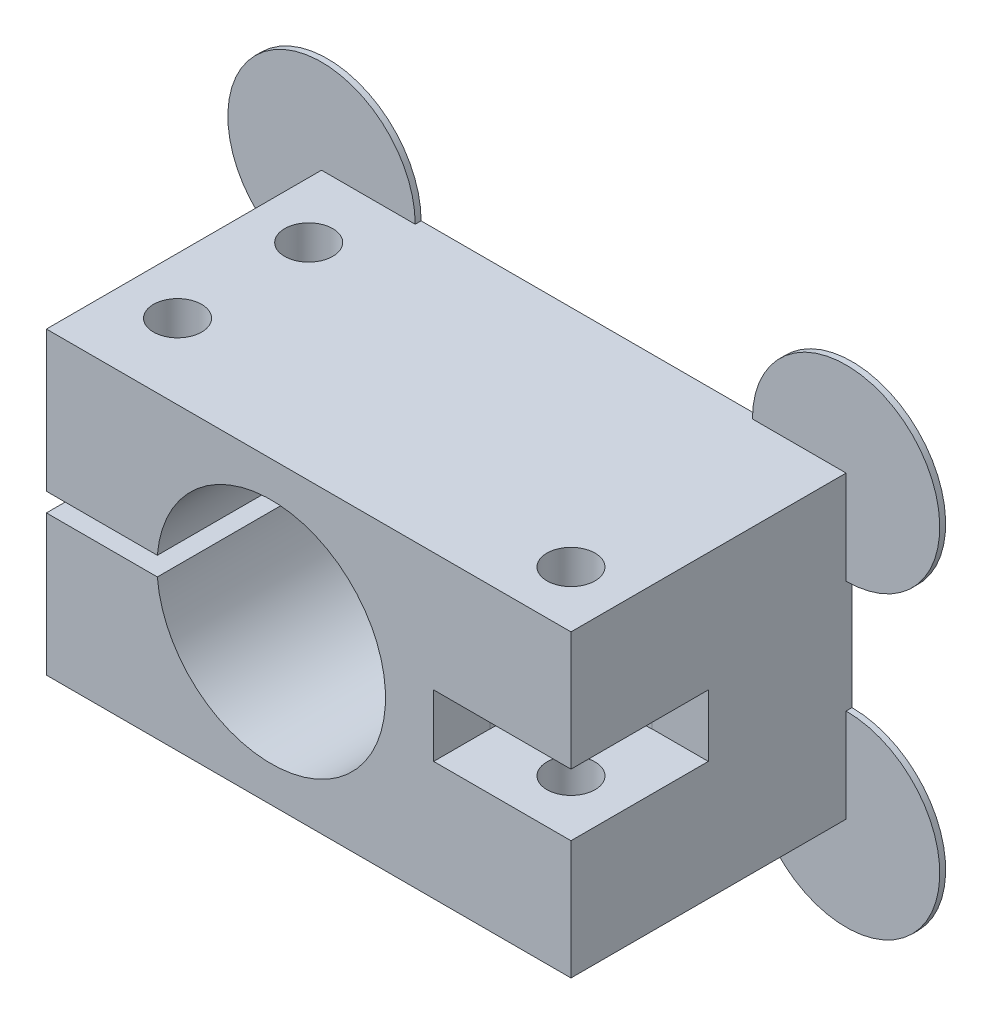
SolidWorks part; units mm, degrees
ref_plane "Front Plane" through (0, 0, 0) normal (0, 0, 1) x (1, 0, 0)
ref_plane "Top Plane" through (0, 0, 0) normal (0, 1, 0) x (1, 0, 0)
ref_plane "Right Plane" through (0, 0, 0) normal (1, 0, 0) x (0, 0, -1)
sketch "Sketch1" plane through (0, 0, 0) normal (0, 0, 1) x (1, 0, 0)
  line L0 (-15.24, 0) -> (20.32, 0) construction
  line L1 (-15.24, -10.16) -> (20.32, -10.16)
  line L2 (-15.24, -10.16) -> (-15.24, 10.16)
  line L3 (-15.24, 10.16) -> (20.32, 10.16)
  line L4 (20.32, -10.16) -> (20.32, 10.16)
  line L5 (0, 10.16) -> (0, -10.16) construction
  point P8 (0, 0)
  dimension "D1" = 20.32
  dimension "D2" = 15.24
  dimension "D3" = 35.56
extrude "Boss-Extrude1" add sketch "Sketch1" along normal blind 19.05
sketch "Sketch2" plane through (0, 0, 19.05) normal (0, 0, 1) x (1, 0, 0)
  circle A0 centre (0, 0) radius 7.747
  dimension "D1" = 15.494
extrude "Cut-Extrude1" cut sketch "Sketch2" against normal through all
sketch "Sketch3" plane through (0, 0, 19.05) normal (0, 0, 1) x (1, 0, 0)
  line L0 (-15.24, 0) -> (-7.747, 0) construction
  line L1 (-15.24, 10.16) -> (-15.24, -10.16) construction
  line L3 (-15.2661, -0.635) -> (-7.7209, -0.635)
  line L4 (-15.2661, -0.635) -> (-15.2661, 0.635)
  line L5 (-15.2661, 0.635) -> (-7.7209, 0.635)
  line L6 (-7.7209, -0.635) -> (-7.7209, 0.635)
  line L7 (-15.2661, -0.635) -> (-7.7209, 0.635) construction
  line L8 (-15.2661, 0.635) -> (-7.7209, -0.635) construction
  circle A0 centre (0, 0) radius 7.747 construction
  point P7 (-11.4935, 0)
  dimension "D1" = 1.27
extrude "Cut-Extrude2" cut sketch "Sketch3" against normal through all
ref_plane "Plane1" through (0, 0, 0) normal (0, 1, 0) x (1, 0, 0)
sketch "Sketch9" plane through (0, 0, 0) normal (0, 1, 0) x (1, 0, 0)
  line L0 (20.32, -19.05) -> (20.32, 0) construction
  line L1 (20.32, -19.05) -> (-15.24, -19.05) construction
  line L2 (11.01, -15.24) -> (11.01, -20.74)
  line L3 (11.01, -20.74) -> (22.01, -20.74)
  line L4 (22.01, -20.74) -> (22.01, -9.74)
  line L5 (22.01, -9.74) -> (16.51, -9.74)
  arc A0 (16.51, -9.74) -> (11.01, -15.24) centre (16.51, -15.24) ccw
  dimension "D1" = 11
  dimension "D2" = 3.81
  dimension "D3" = 3.81
extrude "Cut-Extrude4" cut sketch "Sketch9" against normal mid plane 4.2
hole_wizard "#4 Clearance Hole1" positions "Sketch6" profile "Sketch5" hole size "#4" standard "ANSI Inch" end condition through all
sketch "Sketch6" plane through (0, -10.16, 0) normal (0, -1, 0) x (-1, 0, 0)
  line L0 (11.43, -19.05) -> (11.43, 0) construction
  line L1 (15.24, -19.05) -> (-20.32, -19.05) construction
  line L2 (15.24, 0) -> (-20.32, 0) construction
  line L3 (15.24, -19.05) -> (15.24, 0) construction
  line L4 (-20.32, -19.05) -> (15.24, -19.05) construction
  line L5 (-20.32, -19.05) -> (-20.32, 0) construction
  point P11 (11.43, -13.97)
  point P17 (11.43, -5.08)
  point P20 (-16.51, -15.24)
  dimension "D1" = 3.81
  dimension "D2" = 5.08
  dimension "D3" = 5.08
  dimension "D4" = 3.81
  dimension "D5" = 3.81
sketch "Sketch5" plane through (-11.43, -10.16, 13.97) normal (1, 0, 0) x (0, 0, -1)
  line L0 (0, 0) -> (0, 20.32)
  line L1 (0, 20.32) -> (1.6319, 20.32)
  line L2 (1.6319, 20.32) -> (1.6319, 0)
  line L5 (1.6319, 0) -> (0, 0)
  line L11 (0, -6.35) -> (0, 107.95) construction
  dimension "Thru Hole Dia." = 3.2639
  dimension "Thru Hole Depth" = 20.32
sketch "Sketch12" plane through (0, 0, 0) normal (0, 0, -1) x (-1, 0, 0)
  line L0 (-2.54, -10.16) -> (-2.54, 10.16) construction
  line L1 (15.24, -10.16) -> (-20.32, -10.16) construction
  line L2 (-20.32, 10.16) -> (15.24, 10.16) construction
  line L3 (-20.32, 0) -> (15.24, 0) construction
  line L4 (-20.32, -10.16) -> (-20.32, 10.16) construction
  line L5 (10.4775, 0) -> (-10.4775, 0) construction
  circle A0 centre (15.24, -10.16) radius 6.35
  circle A1 centre (-20.32, -10.16) radius 6.35
  circle A2 centre (-20.32, 10.16) radius 6.35
  circle A3 centre (15.24, 10.16) radius 6.35
  dimension "D1" = 12.7
extrude "Boss-Extrude2" add sketch "Sketch12" against normal blind 0.4
